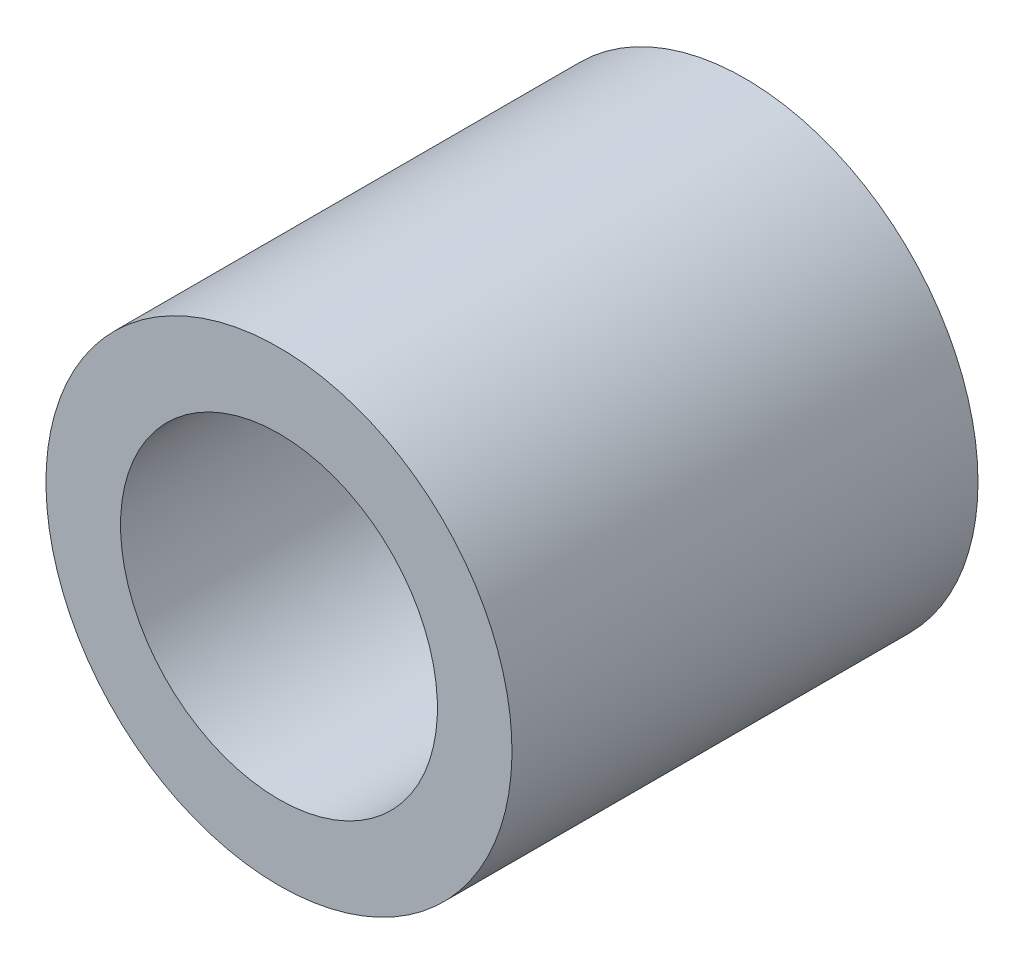
SolidWorks part; units mm, degrees
ref_plane "Plan de face" through (0, 0, 0) normal (0, 0, 1) x (1, 0, 0)
ref_plane "Plan de dessus" through (0, 0, 0) normal (0, 1, 0) x (1, 0, 0)
ref_plane "Plan de droite" through (0, 0, 0) normal (1, 0, 0) x (0, 0, -1)
sketch "Esquisse1" plane through (0, 0, 0) normal (0, 0, 1) x (1, 0, 0)
  circle A1 centre (-20.1526, -28.52) radius 1.7
  circle A2 centre (-20.1526, -28.52) radius 2.5
  dimension "D1" = 5
extrude "Boss.-Extru.1" add sketch "Esquisse1" along normal up to surface (5 mm away)
